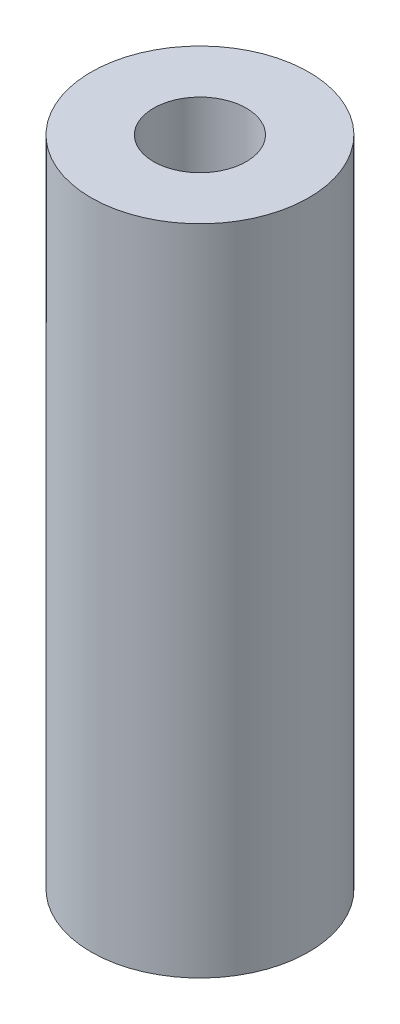
SolidWorks part; units mm, degrees
ref_plane "Front Plane" through (0, 0, 0) normal (0, 0, 1) x (1, 0, 0)
ref_plane "Top Plane" through (0, 0, 0) normal (0, 1, 0) x (1, 0, 0)
ref_plane "Right Plane" through (0, 0, 0) normal (1, 0, 0) x (0, 0, -1)
sketch "Sketch1" plane through (0, 0, 0) normal (0, 1, 0) x (1, 0, 0)
  circle A0 centre (0, 0) radius 3.175
  dimension "D1" = 6.35
extrude "Boss-Extrude1" add sketch "Sketch1" along normal blind 19.05
sketch "Sketch4" plane through (0, 19.05, 0) normal (0, 1, 0) x (1, 0, 0)
  circle A0 centre (0, 0) radius 3.175 construction
  point P0 (0, 0)
sketch "Sketch5" plane through (0, 0, 0) normal (0, -1, 0) x (1, 0, 0)
  circle A0 centre (0, 0) radius 3.175 construction
  point P0 (0, 0)
hole_wizard "Tap Drill for #6-32 Tap1" positions "Sketch9" profile "Sketch8" hole size "#6-32" standard "ANSI Inch" end condition through all
sketch "Sketch9" plane through (0, 19.05, 0) normal (0, 1, 0) x (1, 0, 0)
  point P0 (0, 0)
sketch "Sketch8" plane through (0, 19.05, 0) normal (1, 0, 0) x (0, 0, 1)
  line L0 (0, 0) -> (0, 19.05)
  line L1 (0, 19.05) -> (1.3525, 19.05)
  line L2 (1.3525, 19.05) -> (1.3525, 0)
  line L5 (1.3525, 0) -> (0, 0)
  line L11 (0, -6.35) -> (0, 107.95) construction
  dimension "Thru Hole Dia." = 2.7051
  dimension "Thru Hole Depth" = 19.05
